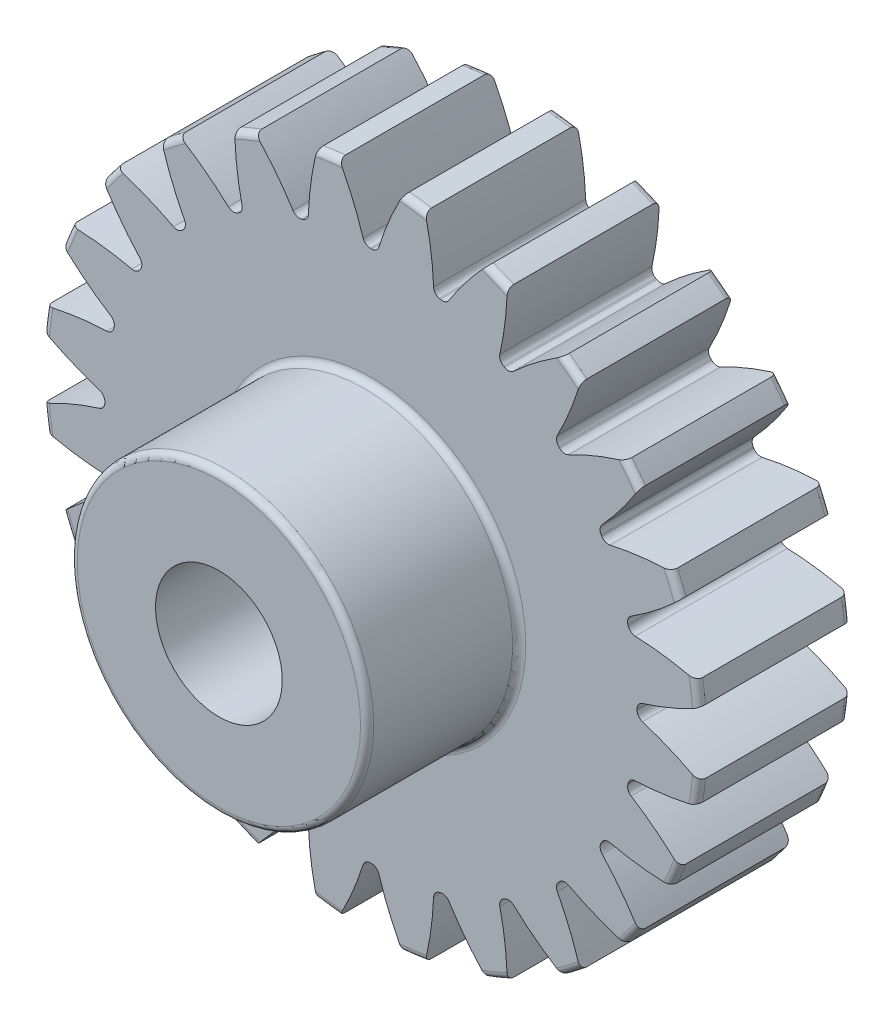
SolidWorks part; units mm, degrees
material "Delrin 2700 NC010, Low Viscosity Acetal Copolymer (SS)"
ref_plane "Front Plane" through (0, 0, 0) normal (0, 0, 1) x (1, 0, 0)
ref_plane "Top Plane" through (0, 0, 0) normal (0, 1, 0) x (1, 0, 0)
ref_plane "Right Plane" through (0, 0, 0) normal (1, 0, 0) x (0, 0, -1)
sketch "Sketch1" plane through (0, 0, 0) normal (0, 0, 1) x (1, 0, 0)
  line L0 (-304.8, 0) -> (304.8, 0) construction
  circle A0 centre (0, 0) radius 13 construction
  circle A1 centre (0, 0) radius 12 construction
  circle A2 centre (0, 0) radius 10.5 construction
  circle A3 centre (0, 0) radius 5.85 construction
  circle A4 centre (0, 0) radius 2.5 construction
  dimension "D2" = 1
  dimension "D3" = 2.5
  dimension "D1" = 2.5
sketch "Sketch2" plane through (0, 0, 0) normal (1, 0, 0) x (0, 0, -1)
  line L0 (0, 0) -> (-6, 0) construction
  line L1 (-6, 0) -> (-12, 0) construction
  dimension "Overall Width" = 12
  dimension "Face Width" = 6
sketch "Sketch4" plane through (0, 0, 0) normal (1, 0, 0) x (0, 0, -1)
  line L0 (-12, 2.5) -> (-12, 5.85)
  line L1 (-12, 5.85) -> (-6, 5.85)
  line L2 (-6, 5.85) -> (-6, 13)
  line L3 (-6, 13) -> (0, 13)
  line L4 (0, 13) -> (0, 2.5)
  line L5 (-6, 5.85) -> (-6, 0) construction
  line L6 (0, 13) -> (0, -13) construction
  line L7 (-6, 5.85) -> (0, 5.85) construction
  line L12 (-12, 2.5) -> (0, 2.5)
revolve "Revolve1" add sketch "Sketch4" angle 360 about L1
fillet "Fillet2" radius 0.26 4 edges at (0, 5.85, 12) (0, 5.85, 6) (0, 13, 6) (0, 13, 0)
sketch "Sketch7" plane through (0, 0, 6) normal (0, 0, 1) x (1, 0, 0)
  line L0 (0, 0) -> (0, 13) construction
  line L1 (0.7848, 11.9743) -> (1.2113, 12.9434) construction
  line L3 (1.6968, 12.8888) -> (1.5663, 11.8973) construction
  line L4 (1.5663, 11.8973) -> (1.3705, 10.4102) construction
  line L5 (0, 0) -> (1.3705, 10.4102) construction
  line L6 (0.7848, 11.9743) -> (0, 0) construction
  line L7 (0.7848, 11.9743) -> (0.8502, 12.9722) construction
  line L8 (0.7848, 11.9743) -> (0, 0) construction
  circle A0 centre (0, 0) radius 13 construction
  arc A1 (-0.0246, 10.5) -> (0.0246, 10.5) centre (0, 0) cw
  circle A2 centre (0, 0) radius 10.5 construction
  arc A3 (-0.7848, 11.9743) -> (0.7848, 11.9743) centre (0, 0) cw construction
  circle A4 centre (0, 0) radius 12 construction
  arc A5 (2.1299, 12.8243) -> (1.2618, 12.9386) centre (0, 0) ccw construction
  arc A6 (0.7848, 11.9743) -> (2.3411, 11.7694) centre (0, 0) cw construction
  arc A7 (-1.2618, 12.9386) -> (1.2618, 12.9386) centre (0, 0) cw
  arc A8 (0.3117, 10.7108) -> (1.2618, 12.9386) centre (11.7686, 7.1413) cw
  arc A9 (-0.3117, 10.7108) -> (-1.2618, 12.9386) centre (-11.7686, 7.1413) ccw
  arc A10 (-0.0246, 10.5) -> (-0.3117, 10.7108) centre (-0.0253, 10.8) cw
  arc A11 (0.0246, 10.5) -> (0.3117, 10.7108) centre (0.0253, 10.8) ccw
  point P26 (-0.2473, 10.4971)
  point P29 (0.2473, 10.4971)
  dimension "D4" = 0.3
  dimension "D5" = 12
  dimension "D3" = 20
  dimension "D1" = 3.1416
  dimension "D2" = 1.5708
extrude "Cut-Extrude2" cut sketch "Sketch7" against normal through all
pattern_circular "CirPattern1" count 24 over 360 about axis through (0, 0, 0) along (0, 0, 1) of "Cut-Extrude2"
equation "\"D1@Sketch1\"=2.5*(\"Pitch Dia.@Sketch1\"/\"Number of Teeth@Sketch1\")"
equation "\"D1@CirPattern1\"=\"Number of Teeth@Sketch1\""
equation "\"D1@Fillet2\"=\"OD@Sketch1\"*.01"
equation "\"D1@Sketch7\"=3.14159*(\"Pitch Dia.@Sketch1\"/\"Number of Teeth@Sketch1\")"
equation "\"D2@Sketch7\"=\"D1@Sketch7\"/2"
equation "\"D4@Sketch7\"=\"D1@Sketch7\"*.0955"
equation "\"D5@Sketch7\"=\"Pitch Dia.@Sketch1\"/2"
